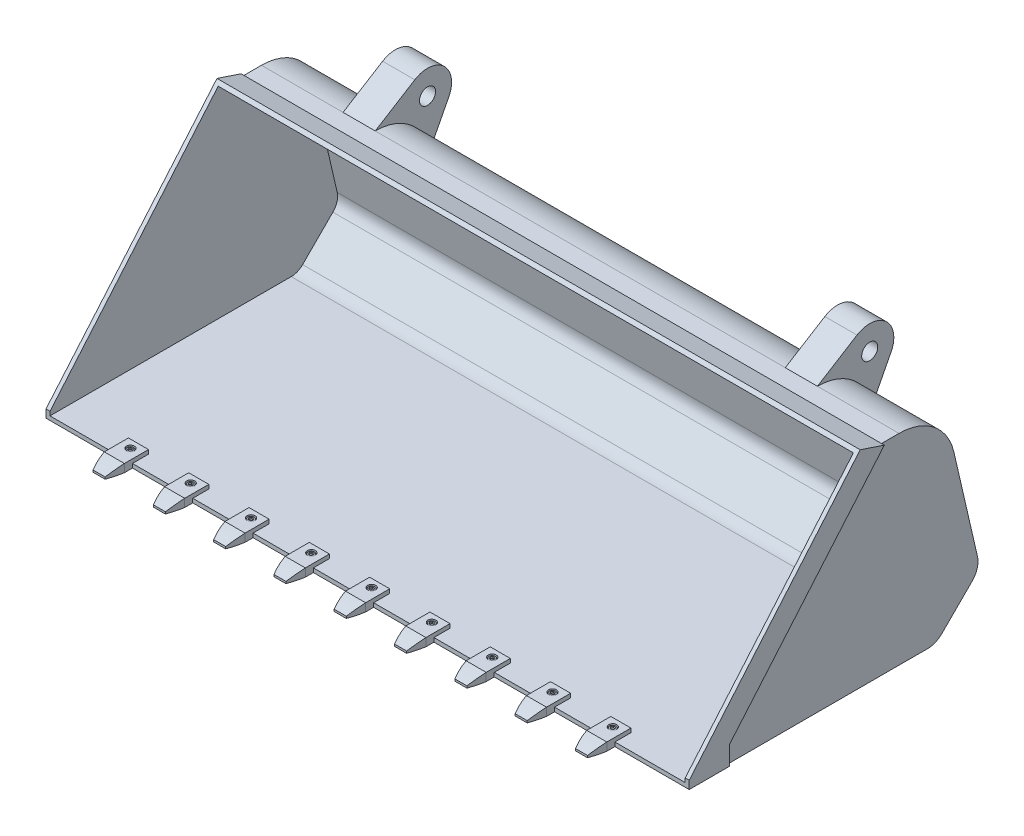
SolidWorks part; units mm, degrees
ref_plane "Front Plane" through (0, 0, 0) normal (0, 0, 1) x (1, 0, 0)
ref_plane "Top Plane" through (0, 0, 0) normal (0, 1, 0) x (1, 0, 0)
ref_plane "Right Plane" through (0, 0, 0) normal (1, 0, 0) x (0, 0, -1)
sketch "Sketch1" plane through (0, 0, 0) normal (1, 0, 0) x (0, 0, -1)
  line L1 (-300, 20) -> (-300, 0)
  line L2 (-300, 0) -> (300, 0)
  line L3 (335.3553, 14.6447) -> (410.7144, 90.0038)
  line L4 (424.0776, 136.6067) -> (365.3826, 390.8427)
  line L5 (228.9708, 499.3496) -> (185.3318, 499.3496)
  line L9 (185.3318, 499.3496) -> (125.3318, 519.3496)
  line L10 (125.3318, 519.3496) -> (-300, 20)
  arc A0 (410.7144, 90.0038) -> (424.0776, 136.6067) centre (375.3591, 125.3591) ccw
  arc A1 (335.3553, 14.6447) -> (300, 0) centre (300, 50) cw
  arc A2 (365.3826, 390.8427) -> (228.9708, 499.3496) centre (228.9708, 359.3496) ccw
  point P10 (430.3122, 109.6016)
  point P13 (320.7107, 0)
  point P16 (340.3318, 499.3496)
  dimension "D9" = 50
  dimension "D11" = 140
  dimension "D1" = 20
  dimension "D2" = 135
  dimension "D3" = 122
  dimension "D4" = 155
  dimension "D5" = 400
  dimension "D6" = 155
  dimension "D7" = 20
  dimension "D8" = 60
  dimension "D10" = 600
extrude "Boss-Extrude1" add sketch "Sketch1" along normal mid plane 1600
sketch "Sketch2" plane through (0, 0, 0) normal (1, 0, 0) x (0, 0, -1)
  line L0 (118.3388, 511.1396) -> (-308.5177, 10)
  line L7 (128.5699, 507.7293) -> (118.3388, 511.1396)
  line L8 (125.3318, 519.3496) -> (-300, 20) construction
  line L10 (300, 10) -> (-308.5177, 10)
  line L14 (414.3339, 134.3571) -> (355.6389, 388.5932)
  line L15 (228.9708, 489.3496) -> (183.709, 489.3496)
  line L16 (183.709, 489.3496) -> (128.5699, 507.7293)
  line L17 (128.5699, 507.7293) -> (-290, 16.3184)
  line L18 (-290, 16.3184) -> (-290, 10)
  line L19 (-290, 10) -> (300, 10)
  line L20 (328.2843, 21.7157) -> (403.6434, 97.0748)
  line L21 (414.3339, 134.3571) -> (355.6389, 388.5932)
  line L22 (228.9708, 489.3496) -> (183.709, 489.3496)
  line L23 (183.709, 489.3496) -> (128.5699, 507.7293)
  line L27 (328.2843, 21.7157) -> (403.6434, 97.0748)
  arc A6 (403.6434, 97.0748) -> (414.3339, 134.3571) centre (375.3591, 125.3591) ccw
  arc A7 (355.6389, 388.5932) -> (228.9708, 489.3496) centre (228.9708, 359.3496) ccw
  arc A8 (300, 10) -> (328.2843, 21.7157) centre (300, 50) ccw
  arc A9 (403.6434, 97.0748) -> (414.3339, 134.3571) centre (375.3591, 125.3591) ccw
  arc A10 (355.6389, 388.5932) -> (228.9708, 489.3496) centre (228.9708, 359.3496) ccw
  arc A11 (300, 10) -> (328.2843, 21.7157) centre (300, 50) ccw
  point P0 (293.4542, 0)
  dimension "D1" = 10
extrude "Cut-Extrude1" cut sketch "Sketch2" against normal mid plane 1580
sketch "Sketch3" plane through (800, 0, 0) normal (1, 0, 0) x (0, 0, -1)
  line L0 (-300, 0) -> (300, 0) construction
  line L1 (335.3553, 14.6447) -> (410.7144, 90.0038) construction
  line L2 (424.0776, 136.6067) -> (365.3826, 390.8427) construction
  line L3 (228.9708, 499.3496) -> (185.3318, 499.3496) construction
  line L4 (-200, 0) -> (300, 0)
  line L5 (335.3553, 14.6447) -> (410.7144, 90.0038)
  line L6 (424.0776, 136.6067) -> (365.3826, 390.8427)
  line L7 (228.9708, 499.3496) -> (185.3318, 499.3496)
  line L8 (185.3318, 499.3496) -> (-200, 46.9609)
  line L9 (-200, 46.9609) -> (-200, 0)
  line L10 (125.3318, 519.3496) -> (-300, 20) construction
  arc A0 (300, 0) -> (335.3553, 14.6447) centre (300, 50) ccw construction
  arc A1 (410.7144, 90.0038) -> (424.0776, 136.6067) centre (375.3591, 125.3591) ccw construction
  arc A2 (365.3826, 390.8427) -> (228.9708, 499.3496) centre (228.9708, 359.3496) ccw construction
  arc A3 (300, 0) -> (335.3553, 14.6447) centre (300, 50) ccw
  arc A4 (410.7144, 90.0038) -> (424.0776, 136.6067) centre (375.3591, 125.3591) ccw
  arc A5 (365.3826, 390.8427) -> (228.9708, 499.3496) centre (228.9708, 359.3496) ccw
  dimension "D1" = 500
extrude "Cut-Extrude2" cut sketch "Sketch3" against normal blind 7
ref_plane "Plane1" through (590, 0, 0) normal (1, 0, 0) x (0, 0, -1)
sketch "Sketch4" plane through (590, 0, 0) normal (1, 0, 0) x (0, 0, -1)
  line L2 (228.9708, 499.3496) -> (327.3558, 560.3446)
  line L3 (412.3015, 481.857) -> (365.3826, 390.8427)
  arc A0 (365.3826, 390.8427) -> (228.9708, 499.3496) centre (228.9708, 359.3496) ccw construction
  arc A1 (365.3826, 390.8427) -> (228.9708, 499.3496) centre (228.9708, 359.3496) ccw
  circle A2 centre (358.9708, 509.3496) radius 20
  arc A3 (327.3558, 560.3446) -> (412.3015, 481.857) centre (358.9708, 509.3496) cw
  dimension "D3" = 40
  dimension "D4" = 60
  dimension "D1" = 150
  dimension "D2" = 130
extrude "Boss-Extrude2" add sketch "Sketch4" against normal blind 80
mirror "Mirror1" about plane through (0, 0, 0) normal (1, 0, 0) of "Cut-Extrude2", "Boss-Extrude2"
sketch "Sketch5" plane through (590, 0, 0) normal (1, 0, 0) x (0, 0, -1)
  line L0 (-260, 20) -> (-260, 10)
  line L1 (-300, 10) -> (300, 10) construction
  line L2 (-260, 10) -> (-300, 10)
  line L3 (-300, 10) -> (-300, 0)
  line L4 (-300, 0) -> (-358.047, 0)
  line L5 (-358.047, 0) -> (-358.047, 5)
  line L7 (-260, 20) -> (-320, 20)
  arc A2 (-358.047, 5) -> (-320, 20) centre (-284.5211, -125.7438) cw
  point P14 (-335.8809, 0)
  point P15 (-270.4837, 20)
  dimension "D4" = 150
  dimension "D1" = 10
  dimension "D2" = 60
  dimension "D3" = 5
  dimension "D5" = 40
extrude "Boss-Extrude3" add sketch "Sketch5" along normal mid plane 50 separate body
sketch "Sketch6" plane through (0, 20, 0) normal (0, 1, 0) x (1, 0, 0)
  line L0 (615, -260) -> (565, -300) construction
  circle A0 centre (590, -280) radius 6
  dimension "D1" = 12
extrude "Cut-Extrude3" cut sketch "Sketch6" against normal through all
sketch "Sketch7" plane through (0, 20, 0) normal (0, 1, 0) x (1, 0, 0)
  circle A0 centre (590, -280) radius 10
  dimension "D1" = 20
extrude "Cut-Extrude4" cut sketch "Sketch7" against normal blind 10
sketch "Sketch8" plane through (0, 10, 0) normal (0, 1, 0) x (1, 0, 0)
  circle A0 centre (590, -280) radius 8.5
  dimension "D1" = 17
extrude "Boss-Extrude4" add sketch "Sketch8" along normal blind 8 separate body
fillet "Fillet1" radius 1 1 edges at (590, 18, 288.5)
sketch "Sketch9" plane through (0, 10, 0) normal (0, 1, 0) x (1, 0, 0)
  circle A0 centre (590, -280) radius 6
  dimension "D1" = 12
extrude "Boss-Extrude5" add sketch "Sketch9" against normal blind 8
sketch "Sketch10" plane through (0, 18, 0) normal (0, 1, 0) x (1, 0, 0)
  line L1 (595.5, -280) -> (592.75, -275.2369)
  line L2 (592.75, -275.2369) -> (587.25, -275.2369)
  line L3 (587.25, -275.2369) -> (584.5, -280)
  line L4 (584.5, -280) -> (587.25, -284.7631)
  line L5 (587.25, -284.7631) -> (592.75, -284.7631)
  line L6 (592.75, -284.7631) -> (595.5, -280)
  circle A0 centre (590, -280) radius 4.7631 construction
  dimension "D1" = 5.5
extrude "Cut-Extrude5" cut sketch "Sketch10" against normal blind 4
sketch "Sketch11" plane through (0, 0, 0) normal (0, -1, 0) x (1, 0, 0)
  line L0 (590, 358.047) -> (590, 328.5881) construction
  line L1 (615, 358.047) -> (565, 358.047) construction
  line L2 (615, 320) -> (623.1283, 320)
  line L3 (565, 320) -> (556.6886, 320)
  line L4 (556.6886, 320) -> (556.6886, 372.3269)
  line L5 (556.6886, 372.3269) -> (623.1283, 372.3269)
  line L6 (623.1283, 372.3269) -> (623.1283, 320)
  line L8 (575, 358.047) -> (605, 358.047)
  arc A0 (565, 320) -> (575, 358.047) centre (780.7075, 283.6427) cw
  arc A1 (615, 320) -> (605, 358.047) centre (399.2925, 283.6427) ccw
  dimension "D2" = 218.75
  dimension "D1" = 30
extrude "Cut-Extrude7" cut sketch "Sketch11" against normal through all
pattern_linear "LPattern2" count 9 spacing 150 along (-1, 0, 0) of bodies 112 113
